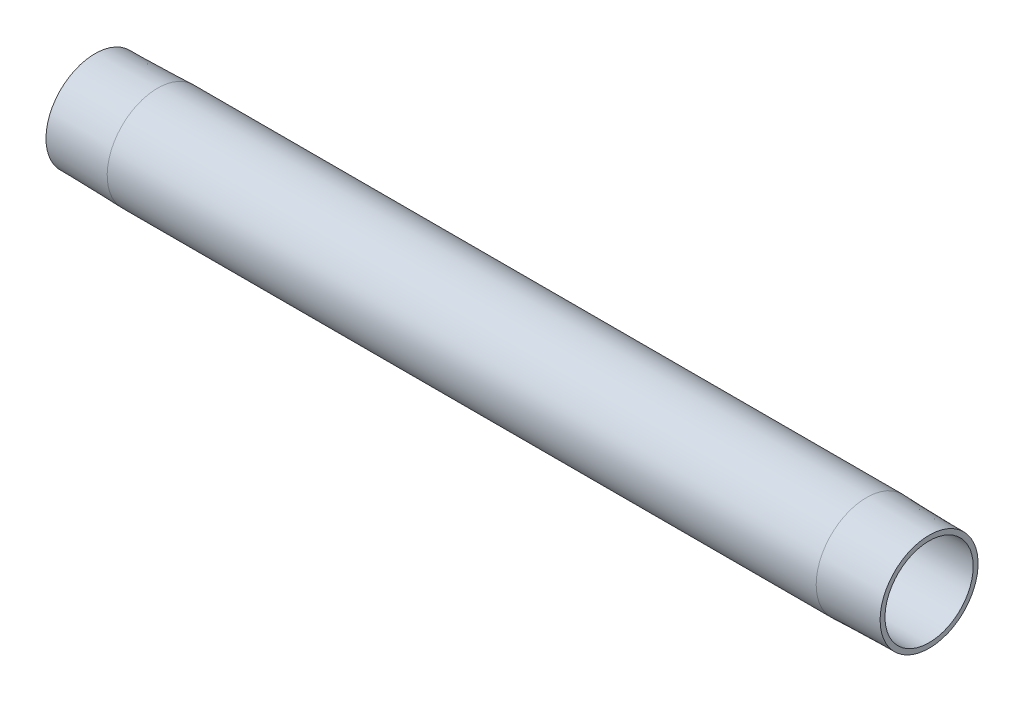
SolidWorks part; units mm, degrees
material "AISI 316 Stainless Steel Sheet (SS)"
ref_plane "Front Plane" through (0, 0, 0) normal (0, 0, 1) x (1, 0, 0)
ref_plane "Top Plane" through (0, 0, 0) normal (0, 1, 0) x (1, 0, 0)
ref_plane "Right Plane" through (0, 0, 0) normal (1, 0, 0) x (0, 0, -1)
sketch "Sketch1" plane through (0, 0, 0) normal (1, 0, 0) x (0, 0, -1)
  circle A0 centre (0, 0) radius 24.15
  circle A1 centre (0, 0) radius 21.15
  dimension "D1" = 48.3
  dimension "D2" = 3
extrude "Boss-Extrude1" add sketch "Sketch1" against normal blind 400
sketch "Sketch2" plane through (0, 0, 0) normal (0, 0, 1) x (1, 0, 0)
  line L0 (0, 24.15) -> (-30, 24.15)
  line L1 (0, 24.15) -> (-400, 24.15) construction
  line L2 (-30, 24.15) -> (0, 23.4954)
  line L3 (0, -24.15) -> (0, 24.15) construction
  line L4 (0, 23.4954) -> (0, 24.15)
  line L5 (0, 0) -> (24.3568, 0) construction
  dimension "D1" = 1.25
  dimension "D2" = 30
revolve "Cut-Revolve1" cut sketch "Sketch2" angle 360 about L5
sketch "Sketch3" plane through (0, 0, 0) normal (0, 0, 1) x (1, 0, 0)
  line L9 (-400, 24.15) -> (-370, 24.15)
  line L10 (-30, 24.15) -> (-400, 24.15) construction
  line L11 (-370, 24.15) -> (-400, 23.4954)
  line L12 (-400, 24.15) -> (-400, -24.15) construction
  line L13 (-400, 23.4954) -> (-400, 24.15)
  line L14 (-400, 0) -> (-363.9965, 0) construction
  dimension "D1" = 30
  dimension "D2" = 1.25
revolve "Cut-Revolve2" cut sketch "Sketch3" angle 360 about L14
